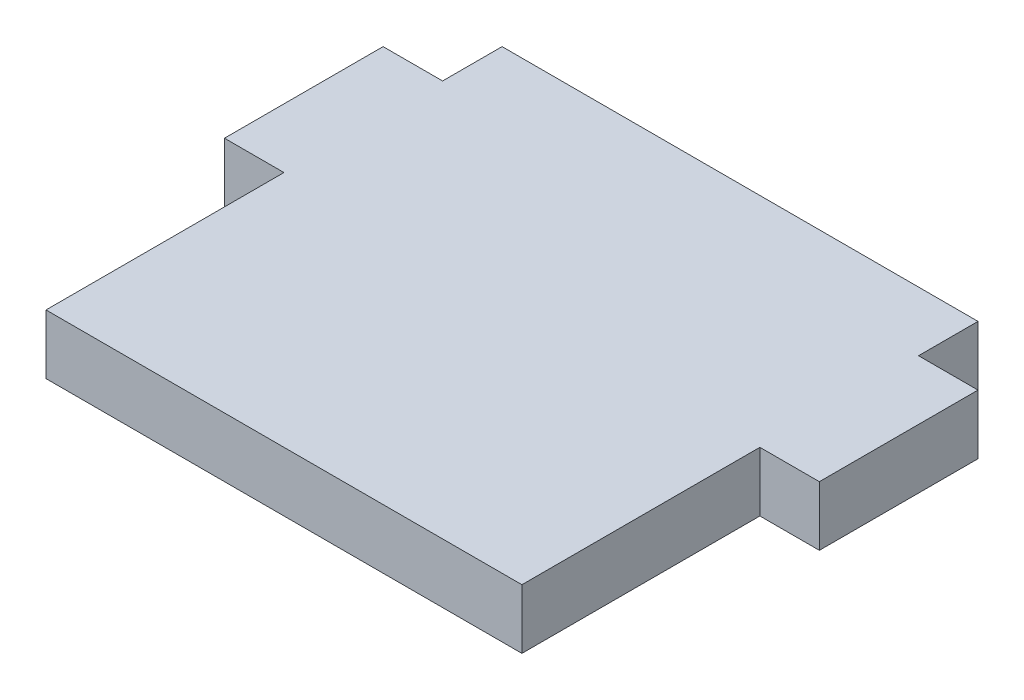
SolidWorks part; units mm, degrees
material "Pine"
ref_plane "Front Plane" through (0, 0, 0) normal (0, 0, 1) x (1, 0, 0)
ref_plane "Top Plane" through (0, 0, 0) normal (0, 1, 0) x (1, 0, 0)
ref_plane "Right Plane" through (0, 0, 0) normal (1, 0, 0) x (0, 0, -1)
sketch "Sketch1" plane through (0, 0, 0) normal (0, 1, 0) x (1, 0, 0)
  line L0 (0, 0) -> (152.4, 0)
  line L1 (152.4, 0) -> (152.4, 76.2)
  line L2 (152.4, 76.2) -> (171.45, 76.2)
  line L3 (171.45, 76.2) -> (171.45, 127)
  line L4 (171.45, 127) -> (152.4, 127)
  line L5 (152.4, 127) -> (152.4, 146.05)
  line L6 (152.4, 146.05) -> (0, 146.05)
  line L7 (0, 146.05) -> (0, 127)
  line L8 (0, 127) -> (-19.05, 127)
  line L9 (-19.05, 127) -> (-19.05, 76.2)
  line L10 (-19.05, 76.2) -> (0, 76.2)
  line L11 (0, 76.2) -> (0, 0)
  dimension "D1" = 152.4
  dimension "D2" = 152.4
  dimension "D3" = 19.05
  dimension "D4" = 50.8
  dimension "D5" = 76.2
  dimension "D6" = 19.05
  dimension "D7" = 19.05
  dimension "D8" = 19.05
  dimension "D9" = 50.8
extrude "Boss-Extrude1" add sketch "Sketch1" along normal blind 19.05
